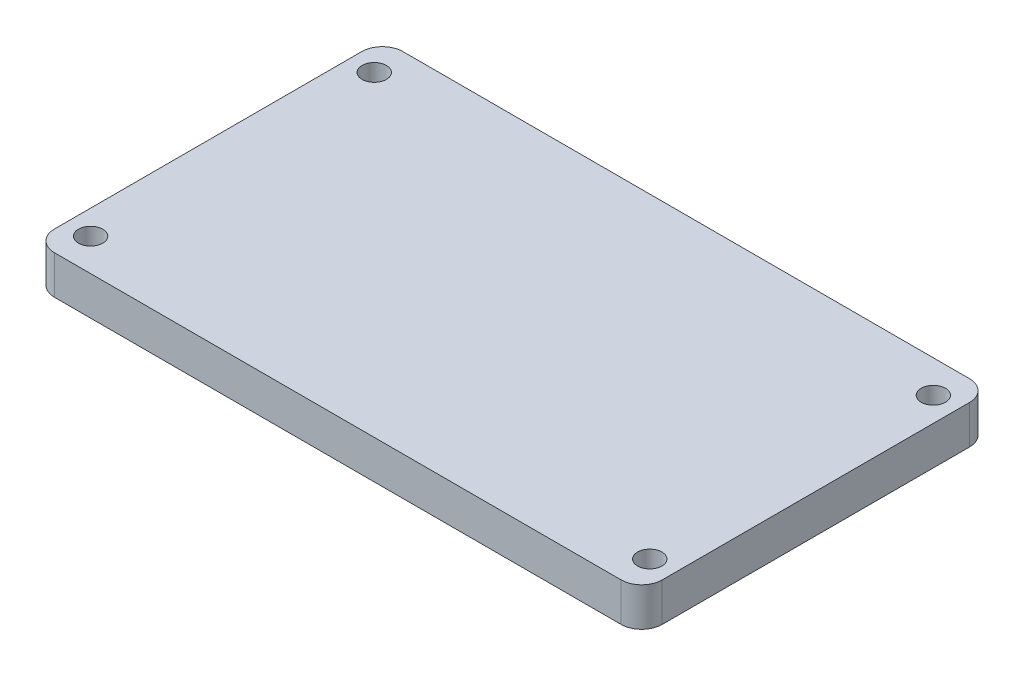
SolidWorks part; units mm, degrees
material "Silicon"
ref_plane "Front Plane" through (0, 0, 0) normal (0, 0, 1) x (1, 0, 0)
ref_plane "Top Plane" through (0, 0, 0) normal (0, 1, 0) x (1, 0, 0)
ref_plane "Right Plane" through (0, 0, 0) normal (1, 0, 0) x (0, 0, -1)
sketch "Sketch1" plane through (0, 0, 0) normal (0, 1, 0) x (1, 0, 0)
  line L0 (-34.5, 17.5) -> (34.5, -17.5) construction
  line L1 (-34.96, -21.5) -> (34.96, -21.5)
  line L2 (-37.5, -18.96) -> (-37.5, 18.96)
  line L3 (-34.96, 21.5) -> (34.96, 21.5)
  line L4 (37.5, -18.96) -> (37.5, 18.96)
  line L5 (-37.5, -21.5) -> (37.5, 21.5) construction
  line L6 (-37.5, 21.5) -> (37.5, -21.5) construction
  line L7 (-34.5, -17.5) -> (34.5, 17.5) construction
  circle A0 centre (-34.5, 17.5) radius 1.5
  circle A1 centre (-34.5, -17.5) radius 1.5
  circle A2 centre (34.5, -17.5) radius 1.5
  circle A3 centre (34.5, 17.5) radius 1.5
  arc A4 (34.96, 21.5) -> (37.5, 18.96) centre (34.96, 18.96) cw
  arc A5 (37.5, -18.96) -> (34.96, -21.5) centre (34.96, -18.96) cw
  arc A6 (-34.96, -21.5) -> (-37.5, -18.96) centre (-34.96, -18.96) cw
  arc A7 (-37.5, 18.96) -> (-34.96, 21.5) centre (-34.96, 18.96) cw
  point P0 (0, 0)
  dimension "D5" = 3
  dimension "D6" = 2.54
  dimension "D1" = 43
  dimension "D2" = 75
  dimension "D3" = 69
  dimension "D4" = 35
extrude "Boss-Extrude1" add sketch "Sketch1" along normal blind 4.7625
